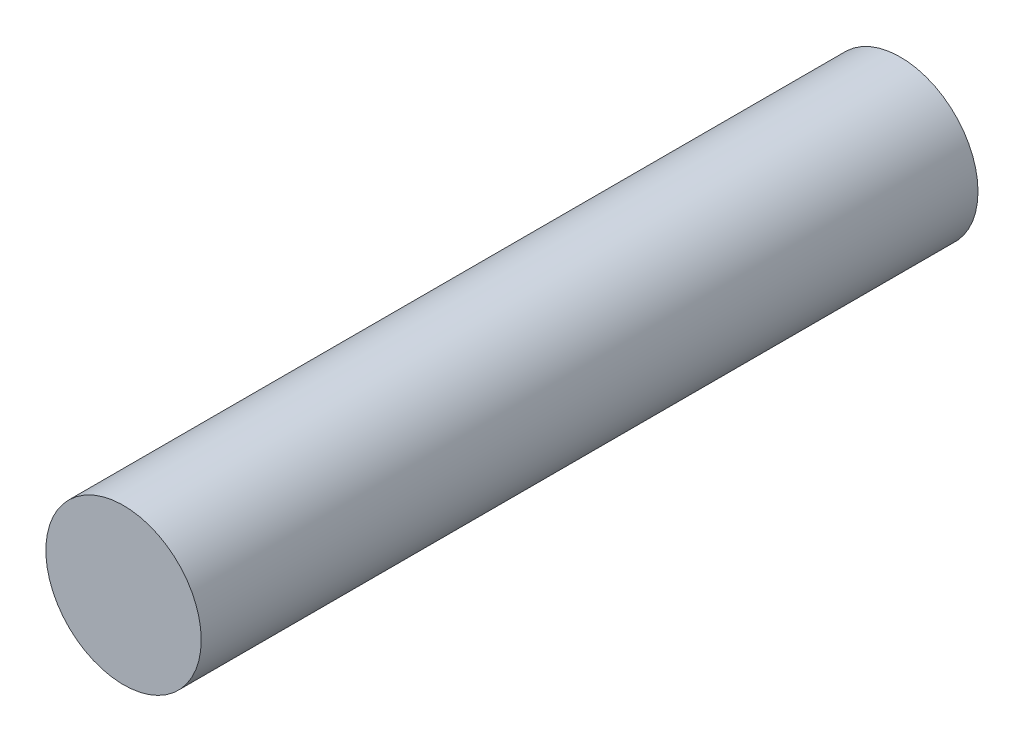
SolidWorks part; units mm, degrees
ref_plane "Alzado" through (0, 0, 0) normal (0, 0, 1) x (1, 0, 0)
ref_plane "Planta" through (0, 0, 0) normal (0, 1, 0) x (1, 0, 0)
ref_plane "Vista lateral" through (0, 0, 0) normal (1, 0, 0) x (0, 0, -1)
sketch "Croquis1" plane through (0, 0, 0) normal (0, 0, 1) x (1, 0, 0)
  circle A0 centre (0, 0) radius 5
  dimension "D1" = 10
extrude "Saliente-Extruir1" add sketch "Croquis1" along normal blind 50
